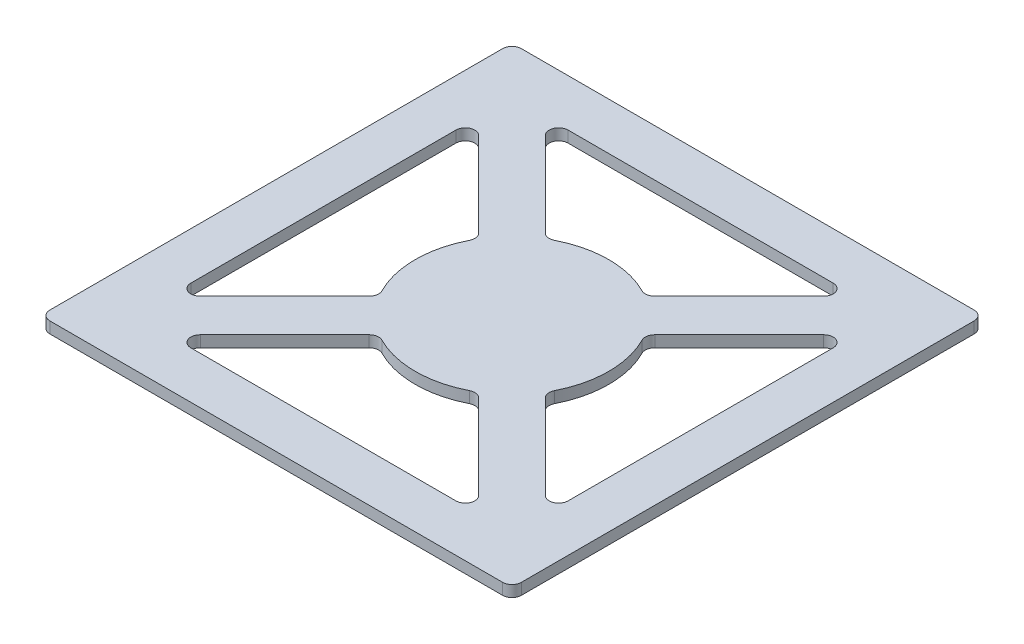
SolidWorks part; units mm, degrees
ref_plane "Front Plane" through (0, 0, 0) normal (0, 0, 1) x (1, 0, 0)
ref_plane "Top Plane" through (0, 0, 0) normal (0, 1, 0) x (1, 0, 0)
ref_plane "Right Plane" through (0, 0, 0) normal (1, 0, 0) x (0, 0, -1)
sketch "Sketch1" plane through (0, 0, 0) normal (0, 1, 0) x (1, 0, 0)
  line L1 (250, -250) -> (-250, -250)
  line L2 (250, -250) -> (250, 250)
  line L3 (250, 250) -> (-250, 250)
  line L4 (-250, -250) -> (-250, 250)
  line L5 (250, -250) -> (-250, 250) construction
  line L6 (250, 250) -> (-250, -250) construction
  point P0 (0, 0)
  dimension "D1" = 500
extrude "Boss-Extrude1" add sketch "Sketch1" along normal blind 12
sketch "Sketch2" plane through (0, 12, 0) normal (0, 1, 0) x (1, 0, 0)
  line L1 (250, 250) -> (17.6777, 17.6777) construction
  line L2 (-200, 164.6447) -> (-88.0914, 52.7361)
  line L3 (164.6447, 200) -> (52.7361, 88.0914)
  line L4 (-164.6447, 200) -> (-52.7361, 88.0914)
  line L5 (200, 164.6447) -> (88.0914, 52.7361)
  line L12 (232.3223, 267.6777) -> (-267.6777, -232.3223) construction
  line L13 (267.6777, 232.3223) -> (-232.3223, -267.6777) construction
  line L14 (-200, 200) -> (-200, -200)
  line L15 (-200, -200) -> (200, -200)
  line L16 (200, -200) -> (200, 200)
  line L17 (200, 200) -> (-200, 200)
  line L18 (-200, 164.6447) -> (-200, -164.6447)
  line L19 (-164.6447, -200) -> (164.6447, -200)
  line L20 (200, -164.6447) -> (200, 164.6447)
  line L21 (164.6447, 200) -> (-164.6447, 200)
  line L22 (-88.0914, -52.7361) -> (-200, -164.6447)
  line L23 (-17.6777, -17.6777) -> (-250, -250) construction
  line L24 (250, 250) -> (-250, -250) construction
  line L25 (-52.7361, -88.0914) -> (-164.6447, -200)
  line L26 (88.0914, -52.7361) -> (200, -164.6447)
  line L28 (52.7361, -88.0914) -> (164.6447, -200)
  arc A0 (88.0914, -52.7361) -> (88.0914, 52.7361) centre (0, 0) ccw
  arc A1 (52.7361, 88.0914) -> (-52.7361, 88.0914) centre (0, 0) ccw
  arc A2 (-88.0914, 52.7361) -> (-88.0914, -52.7361) centre (0, 0) ccw
  arc A3 (-52.7361, -88.0914) -> (52.7361, -88.0914) centre (0, 0) ccw
  dimension "D1" = 25
  dimension "D2" = 25
  dimension "D3" = 50
extrude "Cut-Extrude1" cut sketch "Sketch2" against normal blind 12
fillet "Fillet1" radius 10 20 edges at (-250, 6, 250) (250, 6, 250) (250, 6, -250) (-250, 6, -250) (200, 6, 164.6447) (88.0914, 6, 52.7361) (88.0914, 6, -52.7361) (-164.6447, 6, 200) (-52.7361, 6, 88.0914) (52.7361, 6, 88.0914) (164.6447, 6, 200) (52.7361, 6, -88.0914) (-52.7361, 6, -88.0914) (-164.6447, 6, -200) (164.6447, 6, -200) (-88.0914, 6, -52.7361) (-88.0914, 6, 52.7361) (-200, 6, 164.6447) (-200, 6, -164.6447) (200, 6, -164.6447)
